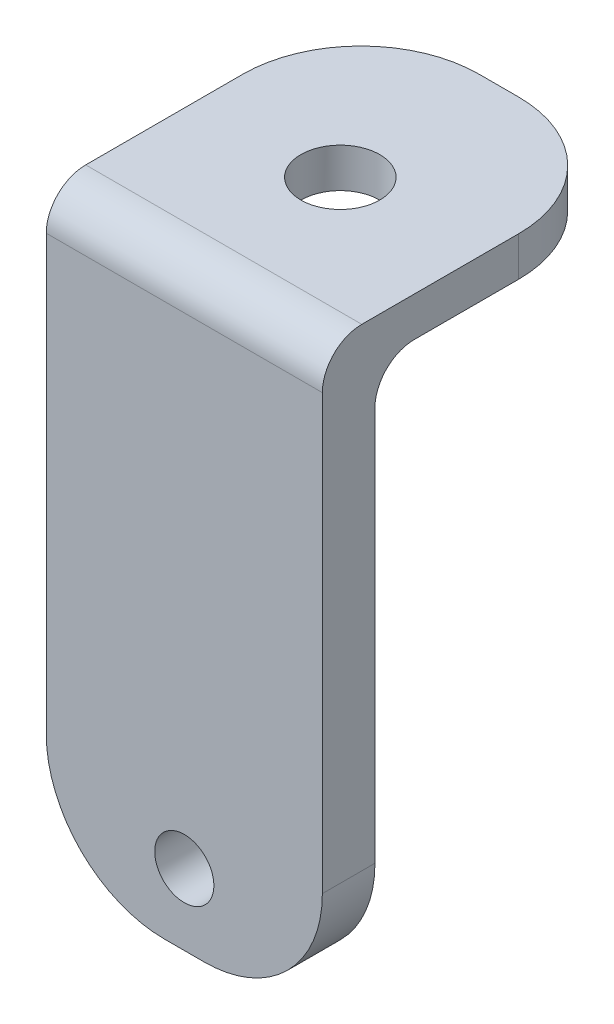
SolidWorks part; units mm, degrees
ref_plane "Front Plane" through (0, 0, 0) normal (0, 0, 1) x (1, 0, 0)
ref_plane "Top Plane" through (0, 0, 0) normal (0, 1, 0) x (1, 0, 0)
ref_plane "Right Plane" through (0, 0, 0) normal (1, 0, 0) x (0, 0, -1)
sketch "Sketch1" plane through (0, 0, 0) normal (1, 0, 0) x (0, 0, -1)
  line L0 (-42.0569, 166.4) -> (-42.0569, 60.2177)
  line L1 (-42.0569, 210.2177) -> (37.732, 210.2177)
  line L2 (-42.0569, 210.2177) -> (-42.0569, 166.4)
  line L3 (-28.717, 200.2177) -> (37.732, 200.2177)
  line L4 (37.732, 210.2177) -> (37.732, 200.2177)
  line L5 (-42.0569, 60.2177) -> (-28.717, 60.2177)
  line L6 (-28.717, 60.2177) -> (-28.717, 200.2177)
  dimension "D1" = 10
  dimension "D2" = 150
extrude "Boss-Extrude1" add sketch "Sketch1" along normal blind 35 and the other way blind 35
sketch "Sketch2" plane through (0, 210.2177, 0) normal (0, 1, 0) x (1, 0, 0)
  line L0 (-35, 37.732) -> (-35, -42.0569) construction
  circle A0 centre (0, -2.5) radius 10
  dimension "D2" = 20
  dimension "D1" = 35
extrude "Cut-Extrude1" cut sketch "Sketch2" against normal blind 35
sketch "Sketch3" plane through (0, 0, 42.0569) normal (0, 0, 1) x (1, 0, 0)
  line L0 (-35, 210.2177) -> (-35, 60.2177) construction
  line L1 (-35, 60.2177) -> (35, 60.2177) construction
  circle A0 centre (0, 78.2177) radius 7.5
  dimension "D2" = 15
  dimension "D1" = 35
  dimension "D3" = 18
extrude "Cut-Extrude2" cut sketch "Sketch3" against normal through all contours A0
fillet "Fillet1" radius 30 4 edges at (-35, 205.2177, -37.732) (35, 205.2177, -37.732) (-35, 60.2177, 35.387) (35, 60.2177, 35.387)
fillet "Fillet2" radius 10 2 edges at (0, 210.2177, 42.0569) (0, 200.2177, 28.717)
